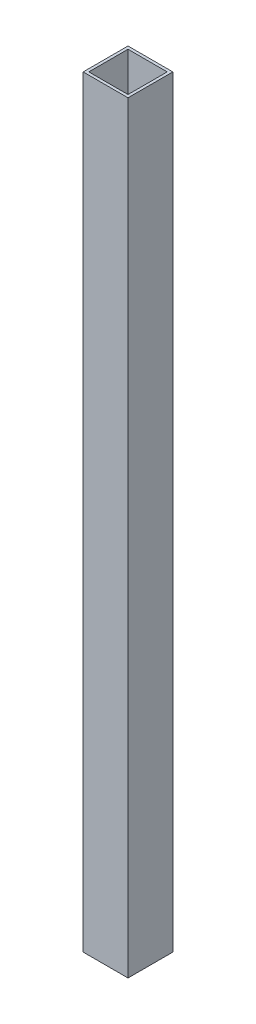
SolidWorks part; units mm, degrees
material "6061-T6 (SS)"
ref_plane "Front Plane" through (0, 0, 0) normal (0, 0, 1) x (1, 0, 0)
ref_plane "Top Plane" through (0, 0, 0) normal (0, 1, 0) x (1, 0, 0)
ref_plane "Right Plane" through (0, 0, 0) normal (1, 0, 0) x (0, 0, -1)
sketch "Sketch1" plane through (0, 0, 0) normal (0, 1, 0) x (1, 0, 0)
  line L0 (11.1125, 11.1125) -> (-11.1125, 11.1125)
  line L1 (12.7, -12.7) -> (-12.7, -12.7)
  line L2 (12.7, -12.7) -> (12.7, 12.7)
  line L3 (12.7, 12.7) -> (-12.7, 12.7)
  line L4 (-12.7, -12.7) -> (-12.7, 12.7)
  line L5 (12.7, -12.7) -> (-12.7, 12.7) construction
  line L6 (12.7, 12.7) -> (-12.7, -12.7) construction
  line L7 (-11.1125, -11.1125) -> (-11.1125, 11.1125)
  line L8 (11.1125, -11.1125) -> (-11.1125, -11.1125)
  line L9 (11.1125, -11.1125) -> (11.1125, 11.1125)
  point P0 (0, 0)
  dimension "D1" = 25.4
  dimension "D2" = 1.5875
extrude "Boss-Extrude1" add sketch "Sketch1" along normal blind 431.8
